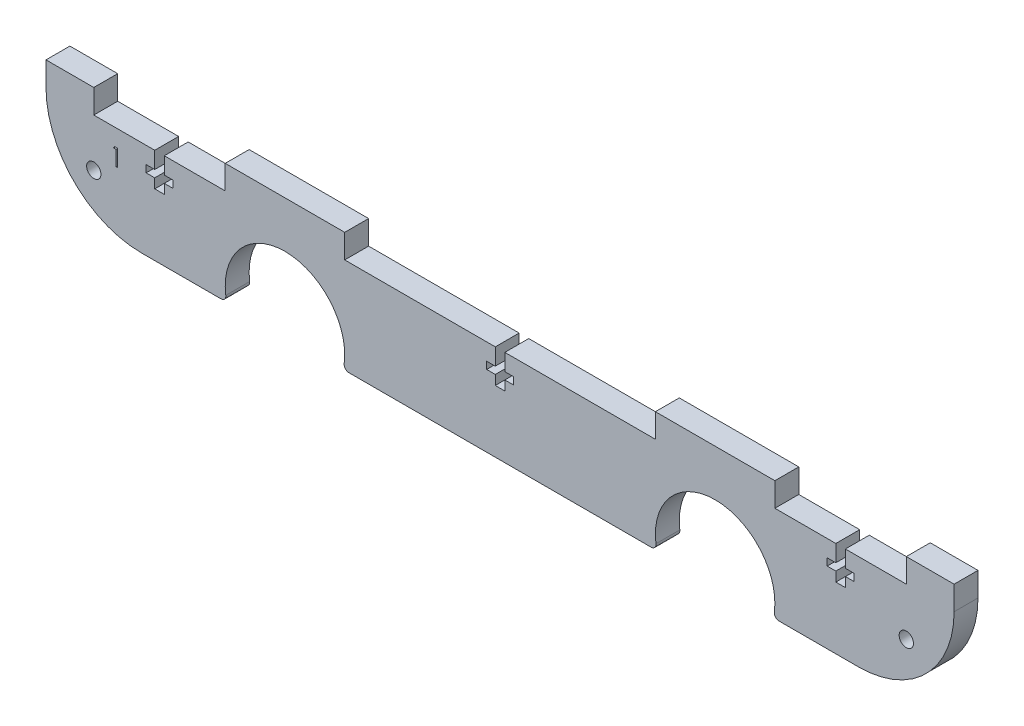
SolidWorks part; units mm, degrees
material "Acrílico (médio-alto impacto)"
ref_plane "Plano frontal" through (0, 0, 0) normal (0, 0, 1) x (1, 0, 0)
ref_plane "Plano superior" through (0, 0, 0) normal (0, 1, 0) x (1, 0, 0)
ref_plane "Plano direito" through (0, 0, 0) normal (1, 0, 0) x (0, 0, -1)
sketch "Esboço1" plane through (0, 0, 0) normal (0, 0, 1) x (1, 0, 0)
  line L2 (20, 0) -> (170, 0)
  line L3 (0, 20) -> (0, 25)
  line L4 (0, 25) -> (190, 25)
  line L5 (190, 20) -> (190, 25)
  arc A0 (190, 20) -> (170, 0) centre (170, 20) cw
  arc A1 (20, 0) -> (0, 20) centre (20, 20) cw
  point P6 (190, 0)
  point P9 (0, 0)
  dimension "D3" = 20
  dimension "D2" = 25
  dimension "D1" = 190
extrude "Ressalto-extrusão1" add sketch "Esboço1" along normal blind 5
sketch "Esboço2" plane through (0, 0, 5) normal (0, 0, 1) x (1, 0, 0)
  line L0 (190, 25) -> (190, -9.7) construction
  line L1 (190, -9.7) -> (0, -9.7) construction
  line L2 (0, -9.7) -> (0, 25) construction
  line L3 (95, 25) -> (95, -9.7) construction
  line L4 (0, 25) -> (190, 25) construction
  line L5 (0, 25) -> (0, 20) construction
  line L6 (190, 2.8) -> (0, 2.8) construction
  circle A0 centre (140, 2.8) radius 12.5
  circle A1 centre (50, 2.8) radius 12.5
  dimension "D1" = 25
  dimension "D2" = 50
extrude "Corte-extrusão1" cut sketch "Esboço2" against normal blind 10
fillet "Filete2" radius 1 4 edges at (152.1824, 0, 2.5) (127.8176, 0, 2.5) (62.1824, 0, 2.5) (37.8176, 0, 2.5)
sketch "Esboço3" plane through (0, 0, 5) normal (0, 0, 1) x (1, 0, 0)
  line L0 (0, 20) -> (200, 20) construction
  line L1 (37.5, 2.8) -> (37.5, 25) construction
  line L2 (0, 25) -> (190, 25) construction
  line L3 (62.5, 2.8) -> (62.5, 25) construction
  line L4 (95, 25) -> (95, 0) construction
  line L6 (63.3795, 0) -> (126.6205, 0) construction
  line L7 (10, 25) -> (10, -4.3224) construction
  line L8 (127.5, 2.8) -> (127.5, 25) construction
  line L9 (152.5, 2.8) -> (152.5, 25) construction
  line L10 (180, 25) -> (180, -4.3224) construction
  line L11 (10, 25) -> (37.5, 25)
  line L12 (10, 25) -> (10, 20)
  line L13 (10, 20) -> (37.5, 20)
  line L14 (37.5, 25) -> (37.5, 20)
  line L15 (62.5, 25) -> (127.5, 25)
  line L16 (62.5, 25) -> (62.5, 20)
  line L17 (62.5, 20) -> (127.5, 20)
  line L18 (127.5, 25) -> (127.5, 20)
  line L19 (152.5, 25) -> (180, 25)
  line L20 (152.5, 25) -> (152.5, 20)
  line L21 (152.5, 20) -> (180, 20)
  line L22 (180, 25) -> (180, 20)
  line L23 (0, 25) -> (0, 20) construction
  arc A0 (62.3884, 1.1333) -> (37.6116, 1.1333) centre (50, 2.8) ccw construction
  line M6 (190, 25) -> (0, 25)
  dimension "D1" = 10
extrude "Corte-extrusão3" cut sketch "Esboço3" against normal through all contours L14 L12 L13 M6 | L18 L16 L17 M6 | L19 L22 L21 L20
sketch "Esboço5" plane through (0, 0, 5) normal (0, 0, 1) x (1, 0, 0)
  line L0 (9.998, 20) -> (37.5, 20) construction
  line L1 (9.998, 20) -> (37.5, 20) construction
  line L2 (10, 20) -> (37.5, 20) construction
  line L3 (152.5, 20) -> (180.002, 20) construction
  line L4 (62.5, 20) -> (127.5, 20) construction
  line L5 (75.75, 20) -> (114.25, 20) construction
  line L6 (62.5, 25) -> (62.5, 20) construction
  line B0 (22.75, 13) -> (22.75, 15)
  line B1 (22.75, 13) -> (24.75, 13)
  line B2 (22.75, 20) -> (24.75, 20)
  line B3 (24.75, 13) -> (24.75, 15)
  line B4 (22.75, 13) -> (24.75, 20) construction
  line B5 (22.75, 20) -> (24.75, 13) construction
  line B6 (23.75, 20) -> (23.75, 11.9737) construction
  line B7 (20.95, 15) -> (22.75, 15)
  line B8 (20.95, 15) -> (20.95, 16.5)
  line B9 (20.95, 16.5) -> (22.75, 16.5)
  line B10 (26.55, 15) -> (26.55, 16.5)
  line B11 (20.95, 15) -> (26.55, 16.5) construction
  line B12 (20.95, 16.5) -> (26.55, 15) construction
  line B13 (24.75, 16.5) -> (24.75, 20)
  line B14 (24.75, 15) -> (26.55, 15)
  line B15 (24.75, 16.5) -> (26.55, 16.5)
  line B16 (22.75, 16.5) -> (22.75, 20)
  line B17 (94, 13) -> (94, 15)
  line B18 (94, 13) -> (96, 13)
  line B19 (94, 20) -> (96, 20)
  line B20 (96, 13) -> (96, 15)
  line B21 (92.2, 15) -> (94, 15)
  line B22 (92.2, 15) -> (92.2, 16.5)
  line B23 (92.2, 16.5) -> (94, 16.5)
  line B24 (97.8, 15) -> (97.8, 16.5)
  line B25 (96, 16.5) -> (96, 20)
  line B26 (96, 15) -> (97.8, 15)
  line B27 (96, 16.5) -> (97.8, 16.5)
  line B28 (94, 16.5) -> (94, 20)
  line B29 (165.251, 13) -> (165.251, 15)
  line B30 (165.251, 13) -> (167.251, 13)
  line B31 (165.251, 20) -> (167.251, 20)
  line B32 (167.251, 13) -> (167.251, 15)
  line B33 (163.451, 15) -> (165.251, 15)
  line B34 (163.451, 15) -> (163.451, 16.5)
  line B35 (163.451, 16.5) -> (165.251, 16.5)
  line B36 (169.051, 15) -> (169.051, 16.5)
  line B37 (167.251, 16.5) -> (167.251, 20)
  line B38 (167.251, 15) -> (169.051, 15)
  line B39 (167.251, 16.5) -> (169.051, 16.5)
  line B40 (165.251, 16.5) -> (165.251, 20)
sketch_block_instance "Bloco1-1"
sketch_block "Bloco1" parameters "D1"=7, "D2"=2, "D3"=5, "D4"=1.5, "D5"=3.5, "D6"=1.5
sketch_block_instance "Bloco1-2"
sketch_block_instance "Bloco1-3"
extrude "Corte-extrusão4" cut sketch "Esboço5" against normal through all
sketch "Esboço6" plane through (0, 0, 5) normal (0, 0, 1) x (1, 0, 0)
  line L0 (95, 0) -> (95, 21.6995) construction
  line L1 (63.3795, 0) -> (126.6205, 0) construction
  line L2 (153.3795, 0) -> (170, 0) construction
  line L3 (190, 20) -> (190, 25) construction
  circle A0 centre (180, 10) radius 1.5
  circle A1 centre (10, 10) radius 1.5
  text T0 "1"
  dimension "D1" = 3
  dimension "D2" = 10
  dimension "D3" = 10
extrude "Corte-extrusão5" cut sketch "Esboço6" against normal through all
